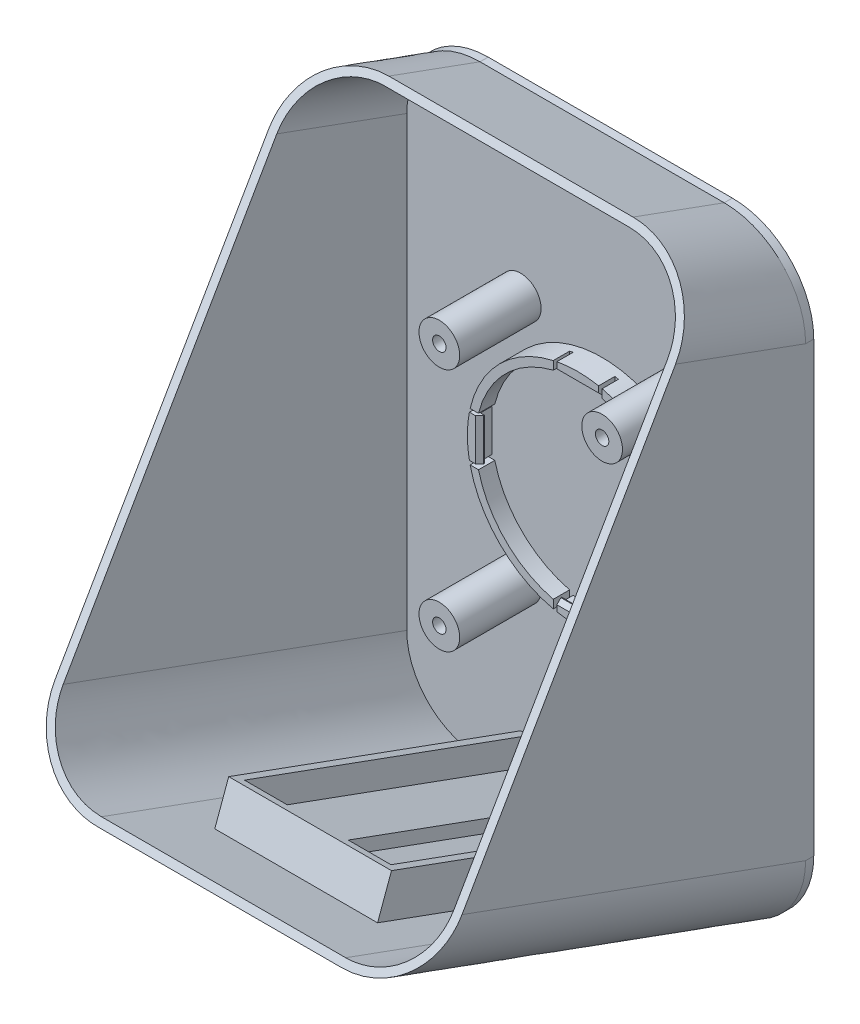
SolidWorks part; units mm, degrees
material "S235JR"
ref_plane "Vorderansicht (XY)" through (0, 0, 0) normal (0, 0, 1) x (1, 0, 0)
ref_plane "Draufansicht (XZ)" through (0, 0, 0) normal (0, 1, 0) x (1, 0, 0)
ref_plane "Seitenansicht (ZY)" through (0, 0, 0) normal (1, 0, 0) x (0, 0, -1)
sketch "Skizze1" plane through (0, 0, 0) normal (0, 0, 1) x (1, 0, 0)
  line L0 (-6, -24.3723) -> (-6, -26.4274)
  line L1 (0, -27.1) -> (0, -25.1) construction
  line L2 (6, -24.3723) -> (6, -26.4274)
  line L3 (-24.3723, 6) -> (-26.4274, 6)
  line L4 (-24.3723, -6) -> (-26.4274, -6)
  line L5 (6, 24.3723) -> (6, 26.4274)
  line L6 (-6, 24.3723) -> (-6, 26.4274)
  line L7 (24.3723, -6) -> (26.4274, -6)
  line L8 (24.3723, 6) -> (26.4274, 6)
  arc A1 (-24.3723, -6) -> (-6, -24.3723) centre (0, 0) ccw
  arc A2 (-26.4274, -6) -> (-6, -26.4274) centre (0, 0) ccw
  arc A3 (-24.3723, 6) -> (-24.3723, -6) centre (0, 0) ccw construction
  arc A4 (-26.4274, 6) -> (-26.4274, -6) centre (0, 0) ccw construction
  arc A5 (6, 24.3723) -> (-6, 24.3723) centre (0, 0) ccw construction
  arc A6 (-6, 24.3723) -> (-24.3723, 6) centre (0, 0) ccw
  arc A7 (6, 26.4274) -> (-6, 26.4274) centre (0, 0) ccw construction
  arc A8 (-6, 26.4274) -> (-26.4274, 6) centre (0, 0) ccw
  arc A9 (24.3723, -6) -> (24.3723, 6) centre (0, 0) ccw construction
  arc A10 (24.3723, 6) -> (6, 24.3723) centre (0, 0) ccw
  arc A11 (26.4274, -6) -> (26.4274, 6) centre (0, 0) ccw construction
  arc A12 (26.4274, 6) -> (6, 26.4274) centre (0, 0) ccw
  arc A13 (0, -25.1) -> (6, -24.3723) centre (0, 0) ccw construction
  arc A14 (6, -24.3723) -> (24.3723, -6) centre (0, 0) ccw
  arc A15 (0, -27.1) -> (6, -26.4274) centre (0, 0) ccw construction
  arc A16 (6, -26.4274) -> (26.4274, -6) centre (0, 0) ccw
  arc A17 (-6, -26.4274) -> (0, -27.1) centre (0, 0) ccw construction
  arc A18 (-6, -24.3723) -> (0, -25.1) centre (0, 0) ccw construction
  point P25 (0, 0)
  dimension "D1" = 2
  dimension "D2" = 50.2
  dimension "D3" = 12
  dimension "D4" = 4
extrude "Aufsatz-Linear austragen1" add sketch "Skizze1" along normal blind 4
sketch "Skizze2" plane through (0, 0, 0) normal (0, 0, -1) x (-1, 0, 0)
  circle A0 centre (0, 0) radius 27.1
  arc A1 (6, -26.4274) -> (26.4274, -6) centre (0, 0) ccw construction
extrude "Aufsatz-Linear austragen2" add sketch "Skizze2" along normal blind 2
sketch "Skizze3" plane through (0, 0, 0) normal (0, 0, 1) x (1, 0, 0)
  line L0 (5.1293, -25.1) -> (-5.1293, -25.1)
  line L1 (-5.1293, -25.1) -> (-5.1293, -26.6102)
  line L2 (0, -25.1) -> (0, -26.6102) construction
  line L3 (5.1293, -25.1) -> (5.1293, -26.6102)
  circle A0 centre (0, 0) radius 25.1
  arc A1 (-6, -26.4274) -> (6, -26.4274) centre (0, 0) ccw construction
  arc A2 (-5.1293, -26.6102) -> (5.1293, -26.6102) centre (0, 0) ccw
extrude "Aufsatz-Linear austragen3" add sketch "Skizze3" along normal up to surface (4 mm away) separate body up to face at (-17.0777, -17.0777, 4)
sketch "Skizze4" plane through (-5.1293, 0, 0) normal (-1, 0, 0) x (0, 0, 1)
  line L0 (4, -25.1) -> (3, -24.1)
  line L1 (3, -24.1) -> (2.8, -24.1)
  line L2 (2.8, -24.1) -> (2.8, -25.1)
  line L4 (4, -26.6102) -> (4, -25.1)
  line L5 (4, -25.1) -> (0, -25.1)
  line L6 (0, -25.1) -> (0, -26.6102)
  line L7 (0, -26.6102) -> (4, -26.6102)
  line L8 (4, -26.6102) -> (4, -25.1) construction
  line L9 (4, -25.1) -> (2.8, -25.1)
  line L11 (0, -26.6102) -> (4, -26.6102) construction
  line L12 (2.8, -25.1) -> (0, -25.1) construction
  line L17 (0, -25.1) -> (0, -26.6102) construction
  dimension "D2" = 45
  dimension "D4" = 1
  dimension "D1" = 0
extrude "Aufsatz-Linear austragen4" add sketch "Skizze4" against normal up to surface (10.2586 mm away) up to face at (5.1293, -25.8551, 2)
pattern_circular "Kreismuster3" count 4 over 360 about axis through (0, 0, 0) along (0, 0, 1) of bodies 108 107
combine bodies "Kombinieren1" operation type add bodies to combine 106 109 110 111 107 113 114 115 108
sketch "Skizze5" plane through (0, 0, -2) normal (0, 0, -1) x (-1, 0, 0)
  line L1 (30, 75) -> (-30, 75)
  line L2 (50, 55) -> (50, -55)
  line L3 (30, -75) -> (-30, -75)
  line L4 (-50, 55) -> (-50, -55)
  line L5 (50, 75) -> (-50, -75) construction
  line L6 (50, -75) -> (-50, 75) construction
  arc A0 (-30, -75) -> (-50, -55) centre (-30, -55) cw
  arc A1 (50, -55) -> (30, -75) centre (30, -55) cw
  arc A2 (30, 75) -> (50, 55) centre (30, 55) cw
  arc A3 (-30, 75) -> (-50, 55) centre (-30, 55) ccw
  point P0 (0, 0)
  dimension "D3" = 20
  dimension "D1" = 100
  dimension "D2" = 150
extrude "Aufsatz-Linear austragen5" add sketch "Skizze5" along normal blind 2
sketch "Skizze6" plane through (0, 0, -2) normal (0, 0, 1) x (1, 0, 0)
  line L0 (48, -55) -> (48, 55)
  line L1 (30, 73) -> (-30, 73)
  line L2 (-48, 55) -> (-48, -55)
  line L3 (-30, -73) -> (30, -73)
  line L4 (50, -55) -> (50, 55)
  line L5 (30, 75) -> (-30, 75)
  line L6 (-50, 55) -> (-50, -55)
  line L7 (-30, -75) -> (30, -75)
  line L8 (50, -55) -> (50, 55)
  line L9 (30, 75) -> (-30, 75)
  line L10 (-50, 55) -> (-50, -55)
  line L11 (-30, -75) -> (30, -75)
  arc A0 (48, 55) -> (30, 73) centre (30, 55) ccw
  arc A1 (-30, 73) -> (-48, 55) centre (-30, 55) ccw
  arc A2 (-48, -55) -> (-30, -73) centre (-30, -55) ccw
  arc A3 (30, -73) -> (48, -55) centre (30, -55) ccw
  arc A4 (30, -75) -> (50, -55) centre (30, -55) ccw
  arc A5 (50, 55) -> (30, 75) centre (30, 55) ccw
  arc A6 (-30, 75) -> (-50, 55) centre (-30, 55) ccw
  arc A7 (-50, -55) -> (-30, -75) centre (-30, -55) ccw
  arc A8 (30, -75) -> (50, -55) centre (30, -55) ccw
  arc A9 (50, 55) -> (30, 75) centre (30, 55) ccw
  arc A10 (-30, 75) -> (-50, 55) centre (-30, 55) ccw
  arc A11 (-50, -55) -> (-30, -75) centre (-30, -55) ccw
  dimension "D1" = 0
  dimension "D2" = 2
sketch "Skizze7" plane through (0, 0, 0) normal (1, 0, 0) x (0, 0, -1)
  line L0 (2, 75) -> (-91.9693, 109.202)
  line L1 (2, 55) -> (2, -55) construction
  line L2 (2, 75) -> (2, 55) construction
  dimension "D1" = 70
  dimension "D2" = 100
sweep "Austragung2" add profiles "Skizze6" path "Skizze7"
sketch "Skizze8" plane through (50, 0, 0) normal (1, 0, 0) x (0, 0, -1)
  line L0 (-91.9693, -40.798) -> (-20.4051, 83.1548)
  line L1 (2, 75) -> (-91.9693, 109.202) construction
  line L2 (-20.4051, 83.1548) -> (-91.9693, 109.202)
  line L3 (-91.9693, 109.202) -> (-91.9693, -66.462)
  line M4 (2, 55) -> (-91.9693, 89.202)
  line M5 (-91.9693, 89.202) -> (-91.9693, -20.798)
  line M6 (-91.9693, -20.798) -> (2, -55)
  dimension "D1" = 30
extrude "Schnitt-Linear austragen1" cut sketch "Skizze8" against normal through all both and the other way through all contours L0 M6 M4 M5 | L2 L3 L0 M4 | L3 L0 M6
sketch "Skizze11" plane through (0, -63.8178, 23.2278) normal (0, 0.9397, -0.342) x (1, 0, 0)
  line L0 (-20, 26.8469) -> (-20, -53.1531)
  line L1 (20, 26.8469) -> (20, -53.1531)
  line L2 (0, 26.8469) -> (0, 12.4362) construction
  line L3 (-20, -53.1531) -> (20, -53.1531)
  line L4 (-30, -72.1377) -> (30, -72.1377)
  line L5 (30, -72.1377) -> (30, 26.8469)
  line L6 (30, 26.8469) -> (-30, 26.8469)
  line L7 (-30, 26.8469) -> (-30, -72.1377)
  line L8 (20, -72.1377) -> (30, -72.1377)
  line L9 (30, -72.1377) -> (30, 26.8469) construction
  line L10 (20, 26.8469) -> (-20, 26.8469)
  line L11 (-30, 26.8469) -> (-30, -72.1377) construction
  line L12 (-20, -53.1531) -> (-20, -72.1377) construction
  line L13 (-20, 26.8469) -> (-30, 26.8469) construction
  line L14 (-30, -72.1377) -> (-20, -72.1377) construction
  line L15 (-20, -72.1377) -> (20, -72.1377) construction
  line L16 (30, 26.8469) -> (20, 26.8469) construction
  line L17 (20, -53.1531) -> (20, -72.1377) construction
  line L18 (-18, -51.1531) -> (18, -51.1531)
  line L19 (18, 24.8469) -> (18, -51.1531)
  line L20 (18, 24.8469) -> (-18, 24.8469)
  line L21 (-18, 24.8469) -> (-18, -51.1531)
  line M11 (30, 26.8469) -> (-30, 26.8469)
  dimension "D2" = 40
  dimension "D3" = 80
  dimension "D1" = 0
  dimension "D4" = 2
extrude "Aufsatz-Linear austragen6" add sketch "Skizze11" along normal blind 10 contours L0 L3 L1 L21 L20 L19 L18 M11
sketch "Skizze12" plane through (0, 18.1794, 49.9476) normal (0, 0.342, 0.9397) x (1, 0, 0)
  line L0 (0, -57.9135) -> (0, -64.0075) construction
  line L1 (-20, -57.9135) -> (20, -57.9135) construction
  line L3 (0, -57.9135) -> (7.5, -57.9135)
  line L4 (0, -57.9135) -> (0, -60.9135)
  line L5 (0, -60.9135) -> (7.5, -60.9135)
  line L6 (7.5, -57.9135) -> (7.5, -60.9135)
  line L7 (0, -57.9135) -> (-7.5, -57.9135)
  line L8 (0, -57.9135) -> (0, -60.9135)
  line L9 (0, -60.9135) -> (-7.5, -60.9135)
  line L10 (-7.5, -57.9135) -> (-7.5, -60.9135)
  line M8 (20, -57.9135) -> (-20, -57.9135)
  dimension "D1" = 15
  dimension "D2" = 3
extrude "Aufsatz-Linear austragen7" add sketch "Skizze12" against normal up to surface (79.5806 mm away) contours L10 L9 L4 M8 | L6 L4 L5 M8
sketch "Skizze13" plane through (50, 0, 0) normal (1, 0, 0) x (0, 0, -1)
  line L0 (4, -47.0005) -> (4, -75)
  line L1 (4, 55) -> (4, -55) construction
  line L2 (4, -75) -> (25.6696, -47.0005)
  line L3 (25.6696, -47.0005) -> (4, -47.0005)
extrude "Schnitt-Linear austragen2" cut sketch "Skizze13" against normal through all both and the other way through all
sketch "Skizze14" plane through (0, -99.8469, -2) normal (0, 0, 1) x (1, 0, 0)
  line L0 (-30, 69.8469) -> (30, 69.8469) construction
  line L1 (-30, 26.8469) -> (-30, 60.7016) construction
  line L2 (30, 26.8469) -> (30, 60.7016) construction
  line L3 (0, 69.8469) -> (0, 99.8469) construction
  line L4 (0, 99.8469) -> (27.7284, 99.8469) construction
  circle A0 centre (-20, 69.8469) radius 5
  circle A2 centre (20, 69.8469) radius 5
  circle A3 centre (-20, 129.8469) radius 5
  circle A4 centre (20, 129.8469) radius 5
  circle A5 centre (0, 99.8469) radius 25.1 construction
  point P9 (-20, 69.8469)
  point P10 (20, 69.8469)
  point P23 (0, 99.4742)
  dimension "D2" = 10
  dimension "D3" = 60
  dimension "D1" = 40
extrude "Aufsatz-Linear austragen8" add sketch "Skizze14" along normal blind 20
hole_wizard "Kernloch für M4 Gewinde1" positions "Skizze15" profile "Skizze17" hole size "M4" standard "DIN"
sketch "Skizze15" plane through (0, 0, 18) normal (0, 0, 1) x (1, 0, 0)
  point P0 (-20, 30)
  point P3 (20, 30)
  point P6 (20, -30)
  point P9 (-20, -30)
sketch "Skizze17" plane through (-20, 30, 18) normal (1, 0, 0) x (0, -1, 0)
  line L0 (0, 0) -> (0, 20.9914)
  line L1 (0, 20.9914) -> (1.65, 20)
  line L2 (1.65, 20) -> (1.65, 0)
  line L5 (1.65, 0) -> (0, 0)
  line L10 (0, 20.9914) -> (-1.65, 20) construction
  line L11 (0, -6.35) -> (0, 107.95) construction
  dimension "Bohrerdurchmesser" = 3.3
  dimension "Bohrungstiefe" = 20
  dimension "Spitzenwinkel" = 118
